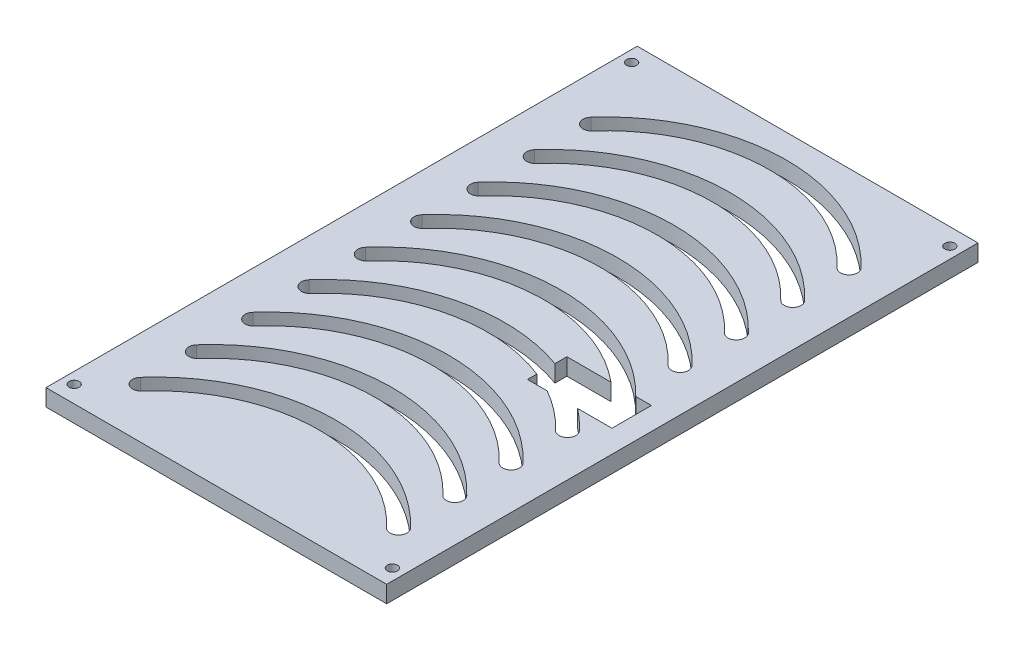
SolidWorks part; units mm, degrees
ref_plane "Front Plane" through (0, 0, 0) normal (0, 0, 1) x (1, 0, 0)
ref_plane "Top Plane" through (0, 0, 0) normal (0, 1, 0) x (1, 0, 0)
ref_plane "Right Plane" through (0, 0, 0) normal (1, 0, 0) x (0, 0, -1)
sketch "Sketch1" plane through (0, 0, 0) normal (0, 1, 0) x (1, 0, 0)
  line L1 (-30.25, 52.5) -> (30.25, 52.5)
  line L2 (-30.25, 52.5) -> (-30.25, -52.5)
  line L3 (-30.25, -52.5) -> (30.25, -52.5)
  line L4 (30.25, 52.5) -> (30.25, -52.5)
  line L5 (-30.25, 52.5) -> (30.25, -52.5) construction
  line L6 (-30.25, -52.5) -> (30.25, 52.5) construction
  point P0 (0, 0)
  dimension "D1" = 60.5
  dimension "D2" = 105
extrude "Boss-Extrude1" add sketch "Sketch1" along normal blind 3
sketch "Sketch2" plane through (0, 3, 0) normal (0, 1, 0) x (1, 0, 0)
  line L0 (-30.25, -52.5) -> (30.25, -52.5) construction
  line L1 (30.25, 52.5) -> (26.25, 52.5)
  line L2 (30.25, 52.5) -> (30.25, -52.5)
  line L3 (30.25, -52.5) -> (26.25, -52.5)
  line L4 (26.25, 52.5) -> (26.25, -52.5)
  line L5 (-30.25, 49.5) -> (-26.25, 49.5)
  line L6 (-30.25, 52.5) -> (-26.25, 52.5)
  line L7 (-30.25, 52.5) -> (-30.25, -52.5)
  line L8 (-30.25, -52.5) -> (-26.25, -52.5)
  line L9 (-26.25, 52.5) -> (-26.25, -52.5)
  line L10 (-30.25, 52.5) -> (30.25, 52.5)
  line L11 (-30.25, 52.5) -> (-30.25, 49.5)
  line L12 (-30.25, 49.5) -> (30.25, 49.5)
  line L13 (30.25, 52.5) -> (30.25, 49.5)
  line L14 (-30.25, -52.5) -> (30.25, -52.5)
  line L15 (-30.25, -52.5) -> (-30.25, -49.5)
  line L16 (-30.25, -49.5) -> (30.25, -49.5)
  line L17 (30.25, -52.5) -> (30.25, -49.5)
  line L18 (0, 49.5) -> (0, 45.3597) construction
  circle A0 centre (-28.25, 49.5) radius 0.9
  circle A1 centre (28.25, 49.5) radius 0.9
  dimension "D1" = 4
  dimension "D2" = 4
extrude "Cut-Extrude1" cut sketch "Sketch2" against normal blind 3 contours A0 | A1
sketch "Sketch4" plane through (0, 3, 0) normal (0, 1, 0) x (1, 0, 0)
  line L0 (30.25, -52.5) -> (30.25, 52.5) construction
  line L1 (-30.25, -52.5) -> (30.25, -52.5) construction
  line L2 (-30.25, -52.5) -> (-30.25, -49.5) construction
  line L4 (30.25, -52.5) -> (30.25, -49.5) construction
  circle A0 centre (-28.25, -49.5) radius 0.9
  circle A1 centre (28.25, -49.5) radius 0.9
extrude "Cut-Extrude2" cut sketch "Sketch4" against normal blind 3
sketch "Sketch5" plane through (0, 3, 0) normal (0, 1, 0) x (1, 0, 0)
  line L7 (26.25, -8.5) -> (11.25, -8.5)
  line L8 (26.25, -8.5) -> (26.25, -1.5)
  line L9 (26.25, -1.5) -> (11.25, -1.5)
  line L10 (11.25, -8.5) -> (11.25, -1.5)
  dimension "D1" = 15
extrude "Cut-Extrude3" cut sketch "Sketch5" against normal blind 3
sketch "Sketch6" plane through (0, 3, 0) normal (0, 1, 0) x (1, 0, 0)
  arc A0 (-22.3431, 36.4581) -> (22.6629, 37.1843) centre (0.4922, 16.2245) cw construction
  arc A1 (23.7529, 38.2148) -> (-23.4658, 37.4529) centre (0.4922, 16.2245) ccw
  arc A2 (21.5729, 36.1539) -> (-21.2204, 35.4634) centre (0.4922, 16.2245) ccw
  arc A3 (21.5729, 36.1539) -> (23.7529, 38.2148) centre (22.6629, 37.1843) ccw
  arc A4 (-23.4658, 37.4529) -> (-21.2204, 35.4634) centre (-22.3431, 36.4581) ccw
  arc A5 (-22.3431, 26.4581) -> (22.6629, 27.1843) centre (0.4922, 6.2245) cw construction
  arc A6 (23.7529, 28.2148) -> (-23.4658, 27.4529) centre (0.4922, 6.2245) ccw
  arc A7 (21.5729, 26.1539) -> (-21.2204, 25.4634) centre (0.4922, 6.2245) ccw
  arc A8 (21.5729, 26.1539) -> (23.7529, 28.2148) centre (22.6629, 27.1843) ccw
  arc A9 (-23.4658, 27.4529) -> (-21.2204, 25.4634) centre (-22.3431, 26.4581) ccw
  arc A10 (-22.3431, 16.4581) -> (22.6629, 17.1843) centre (0.4922, -3.7755) cw construction
  arc A11 (23.7529, 18.2148) -> (-23.4658, 17.4529) centre (0.4922, -3.7755) ccw
  arc A12 (21.5729, 16.1539) -> (-21.2204, 15.4634) centre (0.4922, -3.7755) ccw
  arc A13 (21.5729, 16.1539) -> (23.7529, 18.2148) centre (22.6629, 17.1843) ccw
  arc A14 (-23.4658, 17.4529) -> (-21.2204, 15.4634) centre (-22.3431, 16.4581) ccw
  arc A15 (-22.3431, 6.4581) -> (22.6629, 7.1843) centre (0.4922, -13.7755) cw construction
  arc A16 (23.7529, 8.2148) -> (-23.4658, 7.4529) centre (0.4922, -13.7755) ccw
  arc A17 (21.5729, 6.1539) -> (-21.2204, 5.4634) centre (0.4922, -13.7755) ccw
  arc A18 (21.5729, 6.1539) -> (23.7529, 8.2148) centre (22.6629, 7.1843) ccw
  arc A19 (-23.4658, 7.4529) -> (-21.2204, 5.4634) centre (-22.3431, 6.4581) ccw
  arc A20 (-22.3431, -3.5419) -> (22.6629, -2.8157) centre (0.4922, -23.7755) cw construction
  arc A21 (23.7529, -1.7852) -> (-23.4658, -2.5471) centre (0.4922, -23.7755) ccw
  arc A22 (21.5729, -3.8461) -> (-21.2204, -4.5366) centre (0.4922, -23.7755) ccw
  arc A23 (21.5729, -3.8461) -> (23.7529, -1.7852) centre (22.6629, -2.8157) ccw
  arc A24 (-23.4658, -2.5471) -> (-21.2204, -4.5366) centre (-22.3431, -3.5419) ccw
  arc A25 (-22.3431, -13.5419) -> (22.6629, -12.8157) centre (0.4922, -33.7755) cw construction
  arc A26 (23.7529, -11.7852) -> (-23.4658, -12.5471) centre (0.4922, -33.7755) ccw
  arc A27 (21.5729, -13.8461) -> (-21.2204, -14.5366) centre (0.4922, -33.7755) ccw
  arc A28 (21.5729, -13.8461) -> (23.7529, -11.7852) centre (22.6629, -12.8157) ccw
  arc A29 (-23.4658, -12.5471) -> (-21.2204, -14.5366) centre (-22.3431, -13.5419) ccw
  arc A30 (-22.3431, -23.5419) -> (22.6629, -22.8157) centre (0.4922, -43.7755) cw construction
  arc A31 (23.7529, -21.7852) -> (-23.4658, -22.5471) centre (0.4922, -43.7755) ccw
  arc A32 (21.5729, -23.8461) -> (-21.2204, -24.5366) centre (0.4922, -43.7755) ccw
  arc A33 (21.5729, -23.8461) -> (23.7529, -21.7852) centre (22.6629, -22.8157) ccw
  arc A34 (-23.4658, -22.5471) -> (-21.2204, -24.5366) centre (-22.3431, -23.5419) ccw
  arc A35 (-22.3431, -33.5419) -> (22.6629, -32.8157) centre (0.4922, -53.7755) cw construction
  arc A36 (23.7529, -31.7852) -> (-23.4658, -32.5471) centre (0.4922, -53.7755) ccw
  arc A37 (21.5729, -33.8461) -> (-21.2204, -34.5366) centre (0.4922, -53.7755) ccw
  arc A38 (21.5729, -33.8461) -> (23.7529, -31.7852) centre (22.6629, -32.8157) ccw
  arc A39 (-23.4658, -32.5471) -> (-21.2204, -34.5366) centre (-22.3431, -33.5419) ccw
  arc A40 (-22.3431, -43.5419) -> (22.6629, -42.8157) centre (0.4922, -63.7755) cw construction
  arc A41 (23.7529, -41.7852) -> (-23.4658, -42.5471) centre (0.4922, -63.7755) ccw
  arc A42 (21.5729, -43.8461) -> (-21.2204, -44.5366) centre (0.4922, -63.7755) ccw
  arc A43 (21.5729, -43.8461) -> (23.7529, -41.7852) centre (22.6629, -42.8157) ccw
  arc A44 (-23.4658, -42.5471) -> (-21.2204, -44.5366) centre (-22.3431, -43.5419) ccw
  point P5 (0, 36.7304)
  point P15 (0, 46.7304)
  point P22 (0, 26.7304)
  point P30 (0, 16.7304)
  point P38 (0, 6.7304)
  point P46 (0, -3.2696)
  point P54 (0, -13.2696)
  point P62 (0, -23.2696)
  point P70 (0, -33.2696)
  dimension "D1" = 9
extrude "Cut-Extrude4" cut sketch "Sketch6" against normal blind 3
